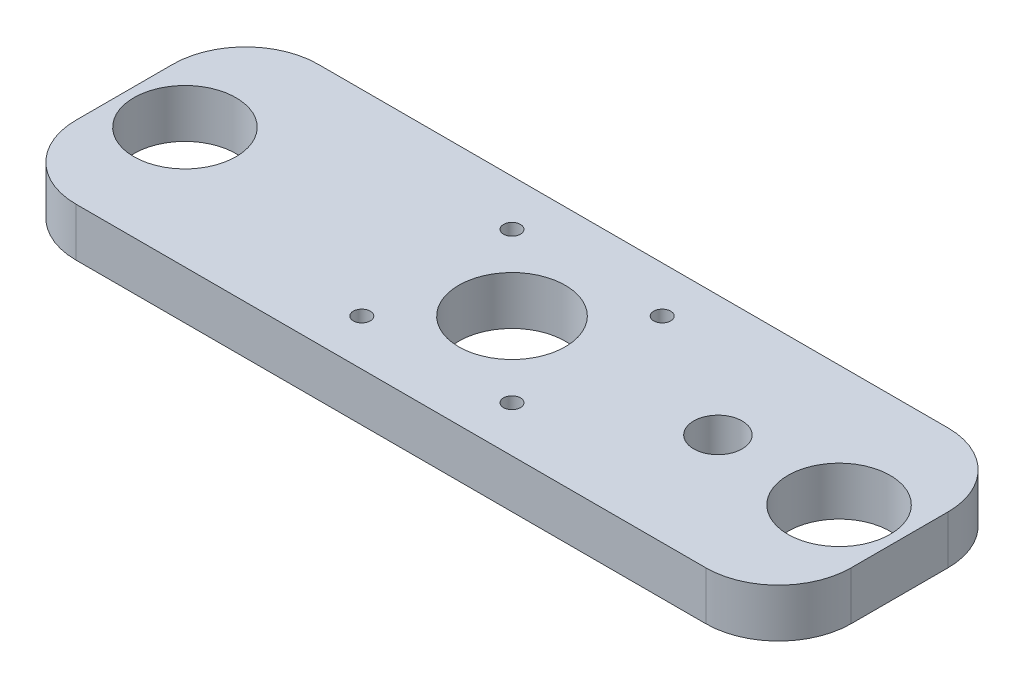
SolidWorks part; units mm, degrees
ref_plane "Front Plane" through (0, 0, 0) normal (0, 0, 1) x (1, 0, 0)
ref_plane "Top Plane" through (0, 0, 0) normal (0, 1, 0) x (1, 0, 0)
ref_plane "Right Plane" through (0, 0, 0) normal (1, 0, 0) x (0, 0, -1)
sketch "Sketch1" plane through (0, 0, 0) normal (0, 1, 0) x (1, 0, 0)
  line L0 (-67.5, 0) -> (67.5, 0) construction
  line L1 (-80, -25) -> (80, -25)
  line L2 (-80, -25) -> (-80, 25)
  line L3 (-80, 25) -> (80, 25)
  line L4 (80, -25) -> (80, 25)
  line L5 (-80, -25) -> (80, 25) construction
  line L6 (-80, 25) -> (80, -25) construction
  line L7 (-15.5, -15.5) -> (15.5, -15.5) construction
  line L8 (-15.5, -15.5) -> (-15.5, 15.5) construction
  line L9 (-15.5, 15.5) -> (15.5, 15.5) construction
  line L10 (15.5, -15.5) -> (15.5, 15.5) construction
  line L11 (-15.5, -15.5) -> (15.5, 15.5) construction
  line L12 (-15.5, 15.5) -> (15.5, -15.5) construction
  circle A0 centre (0, 0) radius 11
  circle A1 centre (15.5, 15.5) radius 1.75
  circle A2 centre (-15.5, 15.5) radius 1.75
  circle A3 centre (-15.5, -15.5) radius 1.75
  circle A4 centre (15.5, -15.5) radius 1.75
  circle A5 centre (-67.5, 0) radius 10.55
  circle A6 centre (67.5, 0) radius 10.55
  circle A7 centre (42.5, 0) radius 5
  point P0 (0, 0)
  point P21 (0, 0)
  dimension "D3" = 22
  dimension "D5" = 3.5
  dimension "D7" = 21.1
  dimension "D8" = 10
  dimension "D9" = 25
  dimension "D1" = 160
  dimension "D2" = 50
  dimension "D4" = 31
  dimension "D6" = 135
extrude "Boss-Extrude1" add sketch "Sketch1" along normal blind 10
fillet "Fillet1" radius 15 4 edges at (80, 5, 25) (80, 5, -25) (-80, 5, -25) (-80, 5, 25)
